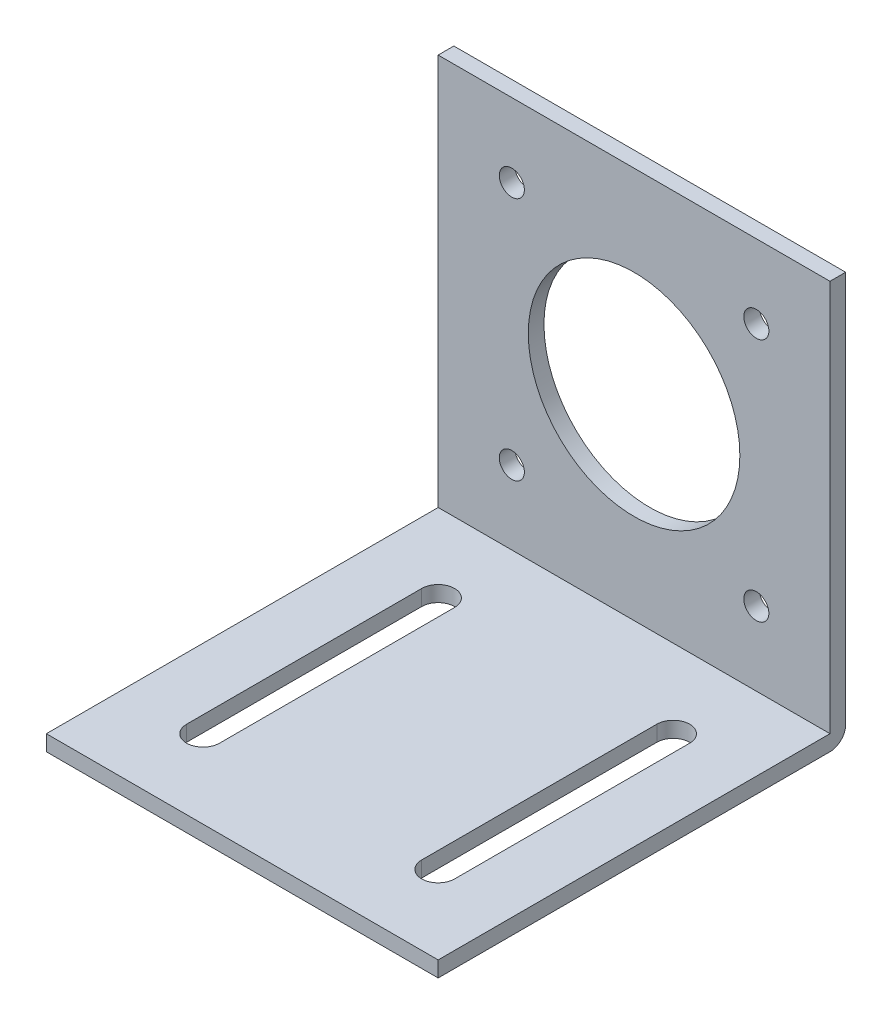
SolidWorks part; units mm, degrees
ref_plane "Front Plane" through (0, 0, 0) normal (0, 0, 1) x (1, 0, 0)
ref_plane "Top Plane" through (0, 0, 0) normal (0, 1, 0) x (1, 0, 0)
ref_plane "Right Plane" through (0, 0, 0) normal (1, 0, 0) x (0, 0, -1)
sketch "Sketch1" plane through (0, 0, 0) normal (0, 1, 0) x (1, 0, 0)
  line L0 (15, 0) -> (-15, 0) construction
  line L1 (-25, -25) -> (25, -25)
  line L2 (-25, -25) -> (-25, 25)
  line L3 (-25, 25) -> (25, 25)
  line L4 (25, -25) -> (25, 25)
  line L5 (-25, -25) -> (25, 25) construction
  line L6 (-25, 25) -> (25, -25) construction
  line L7 (-15, -15) -> (-15, 15) construction
  line L8 (-17.1, 15) -> (-17.1, -15)
  line L9 (-12.9, 15) -> (-12.9, -15)
  line L10 (0, 0) -> (0, 9.909) construction
  line L11 (17.1, 15) -> (17.1, -15)
  line L12 (12.9, 15) -> (12.9, -15)
  arc A0 (-12.9, 15) -> (-17.1, 15) centre (-15, 15) ccw
  arc A1 (-17.1, -15) -> (-12.9, -15) centre (-15, -15) ccw
  arc A2 (12.9, 15) -> (17.1, 15) centre (15, 15) cw
  arc A3 (17.1, -15) -> (12.9, -15) centre (15, -15) cw
  point P0 (0, 0)
  point P9 (0, 0)
  point P12 (-15, 0)
  dimension "D5" = 4.2
  dimension "D6" = 4.2
  dimension "D1" = 50
  dimension "D2" = 50
  dimension "D3" = 30
  dimension "D4" = 30
extrude "Boss-Extrude1" add sketch "Sketch1" along normal blind 2
sketch "Sketch2" plane through (0, 0, 0) normal (0, -1, 0) x (1, 0, 0)
  line L1 (25, -25) -> (-25, -25)
  line L2 (25, -25) -> (25, -27)
  line L3 (25, -27) -> (-25, -27)
  line L4 (-25, -25) -> (-25, -27)
  dimension "D1" = 2
extrude "Boss-Extrude2" add sketch "Sketch2" against normal blind 52
sketch "Sketch3" plane through (0, 0, -25) normal (0, 0, 1) x (1, 0, 0)
  line L0 (-25, 52) -> (25, 2) construction
  line L2 (15.6, 11.4) -> (-15.6, 11.4) construction
  line L3 (15.6, 11.4) -> (15.6, 42.6) construction
  line L4 (15.6, 42.6) -> (-15.6, 42.6) construction
  line L5 (-15.6, 11.4) -> (-15.6, 42.6) construction
  line L6 (15.6, 11.4) -> (-15.6, 42.6) construction
  line L7 (15.6, 42.6) -> (-15.6, 11.4) construction
  circle A0 centre (-15.6, 42.6) radius 1.6
  circle A1 centre (15.6, 42.6) radius 1.6
  circle A2 centre (15.6, 11.4) radius 1.6
  circle A3 centre (-15.6, 11.4) radius 1.6
  circle A4 centre (0, 27) radius 13.5
  point P4 (0, 27)
  dimension "D3" = 3.2
  dimension "D6" = 27
  dimension "D1" = 31.2
  dimension "D2" = 31.2
  dimension "D4" = 2
  dimension "D5" = 2
extrude "Cut-Extrude1" cut sketch "Sketch3" against normal up to next
fillet "Fillet1" radius 2 1 edges at (0, 0, -27)
